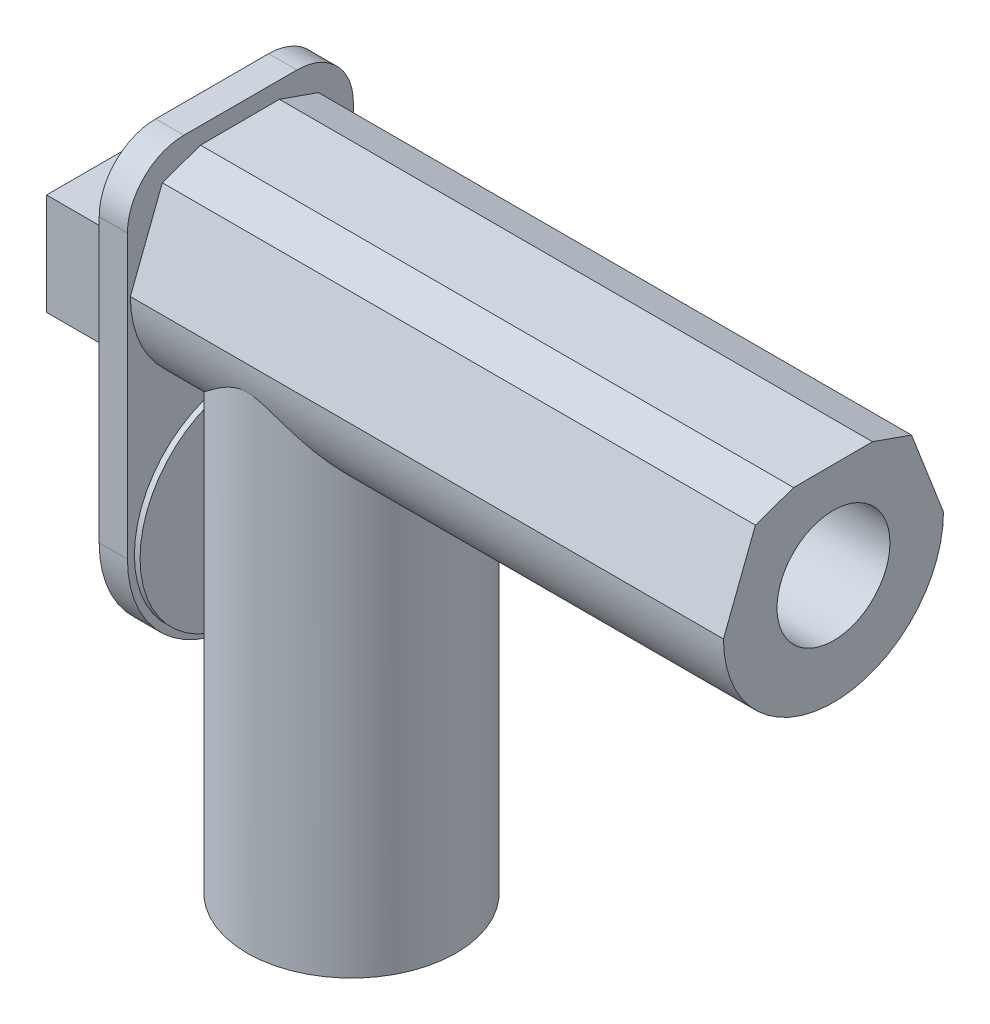
SolidWorks part; units mm, degrees
ref_plane "前视基准面" through (0, 0, 0) normal (0, 0, 1) x (1, 0, 0)
ref_plane "上视基准面" through (0, 0, 0) normal (0, 1, 0) x (1, 0, 0)
ref_plane "右视基准面" through (0, 0, 0) normal (1, 0, 0) x (0, 0, -1)
sketch "草图1" plane through (0, 0, 0) normal (0, 0, 1) x (1, 0, 0)
  line L0 (-2.7226, 51.4621) -> (16.2774, 51.4621)
  line L1 (16.2774, 51.4621) -> (16.2774, 33.4621)
  line L2 (-2.7226, 51.4621) -> (-2.7226, 33.4621)
  line L3 (-2.7226, 33.4621) -> (16.2774, 33.4621)
  line L4 (6.7774, 51.4621) -> (6.7774, 33.4621) construction
extrude "凸台-拉伸1" add sketch "草图1" along normal blind 20
sketch "草图2" plane through (16.2774, 0, 0) normal (1, 0, 0) x (0, 0, -1)
  line L0 (-20, 51.4621) -> (0.648, 33.4621) construction
  line L1 (-29.676, 12.4621) -> (-29.676, 42.4621)
  line L2 (-20, 33.4621) -> (0, 33.4621) construction
  line L3 (10.324, 42.4621) -> (-29.676, 42.4621) construction
  line L4 (-29.676, 42.4621) -> (-29.676, 62.4621)
  line L5 (-19.676, 72.4621) -> (0.324, 72.4621)
  line L12 (10.324, 62.4621) -> (10.324, 42.4621)
  line L13 (10.324, 42.4621) -> (10.324, 12.4621)
  arc A1 (10.324, 62.4621) -> (0.324, 72.4621) centre (0.324, 62.4621) ccw
  arc A2 (-29.676, 62.4621) -> (-19.676, 72.4621) centre (-19.676, 62.4621) cw
  arc A3 (-29.676, 12.4621) -> (10.324, 12.4621) centre (-9.676, 12.4621) ccw
  point P8 (-9.676, 42.4621)
  point P11 (-29.676, 42.4621)
  dimension "D1" = 10
extrude "凸台-拉伸2" add sketch "草图2" along normal blind 5
sketch "草图4" plane through (21.2774, 0, 0) normal (1, 0, 0) x (0, 0, -1)
  line L0 (-29.676, 12.4621) -> (10.324, 12.4621) construction
  arc A0 (-29.676, 12.4621) -> (10.324, 12.4621) centre (-9.676, 12.4621) ccw construction
  circle A1 centre (-9.676, 12.4621) radius 18.7656
extrude "凸台-拉伸4" add sketch "草图4" along normal blind 1
sketch "草图5" plane through (21.2774, 0, 0) normal (1, 0, 0) x (0, 0, -1)
  line L0 (-9.676, 72.4621) -> (-9.676, 71.9404) construction
  line L1 (0.324, 72.4621) -> (-19.676, 72.4621) construction
  line L2 (-29.1544, 52.4621) -> (9.8023, 52.4621) construction
  line L3 (-29.1544, 52.4621) -> (-23.4967, 67.0836)
  line L4 (-23.4967, 67.0836) -> (-16.7253, 69.4632)
  line L5 (9.8023, 52.4621) -> (4.1447, 67.0836)
  line L6 (4.1447, 67.0836) -> (-2.7657, 69.512)
  line L7 (-16.7253, 69.4632) -> (-2.7657, 69.512)
  arc A0 (-29.1544, 52.4621) -> (9.8023, 52.4621) centre (-9.676, 52.4621) ccw
extrude "凸台-拉伸5" add sketch "草图5" along normal blind 105
sketch "草图6" plane through (126.2774, 0, 0) normal (1, 0, 0) x (0, 0, -1)
  line L0 (-29.1544, 52.4621) -> (9.8023, 52.4621) construction
  line L1 (-23.4967, 67.0836) -> (-29.1544, 52.4621) construction
  line L2 (-23.4967, 67.0836) -> (-29.1544, 52.4621) construction
  circle A0 centre (-9.676, 52.4621) radius 10
sketch "草图10" plane through (0, 33.4621, 0) normal (0, -1, 0) x (1, 0, 0)
  line L0 (16.2774, 10) -> (41.2774, 10) construction
  line L1 (16.2774, 20) -> (16.2774, 0) construction
  circle A0 centre (41.2774, 10) radius 20
ref_plane "基准面5" through (0, 32.4621, 0) normal (0, -1, 0) x (-1, 0, 0)
sketch "草图12" plane through (0, 51.4621, 0) normal (0, 1, 0) x (1, 0, 0)
  circle A0 centre (41.2774, -10) radius 18.5
extrude "凸台-拉伸13" add sketch "草图12" against normal blind 90
sketch "草图13" plane through (0, 33.4621, 0) normal (0, -1, 0) x (1, 0, 0)
  line L0 (7.557, 20) -> (7.557, 0) construction
  line L1 (-2.7226, 20) -> (16.2774, 20) construction
  line L2 (-2.7226, 0) -> (16.2774, 0) construction
  circle A0 centre (7.557, 10) radius 3.5
extrude "切除-拉伸2" cut sketch "草图13" against normal blind 40 and the other way blind 20
extrude "切除-拉伸3" cut sketch "草图6" against normal blind 100
